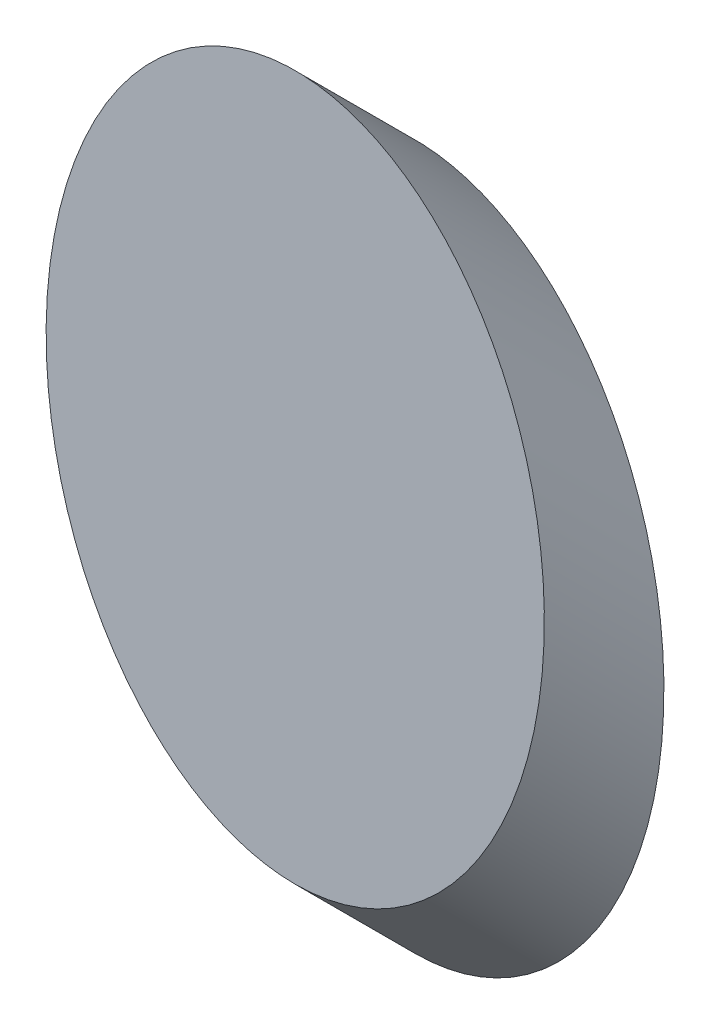
SolidWorks part; units mm, degrees
ref_plane "前视基准面" through (0, 0, 0) normal (0, 0, 1) x (1, 0, 0)
ref_plane "上视基准面" through (0, 0, 0) normal (0, 1, 0) x (1, 0, 0)
ref_plane "右视基准面" through (0, 0, 0) normal (1, 0, 0) x (0, 0, -1)
sketch "草图1" plane through (0, 0, 0) normal (0, 0, 1) x (1, 0, 0)
  ellipse E0 centre (54.3924, 35.7889) end of major axis (54.3924, 18.1089) minor radius 12.5
  dimension "D1" = 25
  dimension "D2" = 35.36
sketch3d "3D草图2"
  line L0 (55.1123, 18.1382, 0) -> (55.1123, 18.1382, -2.7888)
  line L3 (55.1123, 18.1382, 0) -> (55.1123, 31.3541, 13.2159)
  line L4 (55.1123, 18.1382, 0) -> (55.1123, 28.9476, 0)
  spline S2 degree 3 poles (54.3924, 18.1089, 0) (79.3924, 18.1089, 0) (79.3924, 53.4689, 0) (54.3924, 53.4689, 0) (29.3924, 53.4689, 0) (29.3924, 18.1089, 0) (54.3924, 18.1089, 0) (79.3924, 18.1089, 0) (79.3924, 53.4689, 0) knots -0.5 0 0 0 0.5 0.5 0.5 1 1 1 1.5 1.5 1.5 weights 1 0.333333 0.333333 1 0.333333 0.333333 1 0.333333 0.333333 only from (54.3924, 18.1089, 0) to (54.3924, 18.1089, 0) construction
  dimension "D1" = 45
extrude "凸台-拉伸2" add sketch "草图1" along direction (0, 0.7071, 0.7071) on the side against the normal blind 8.4853
